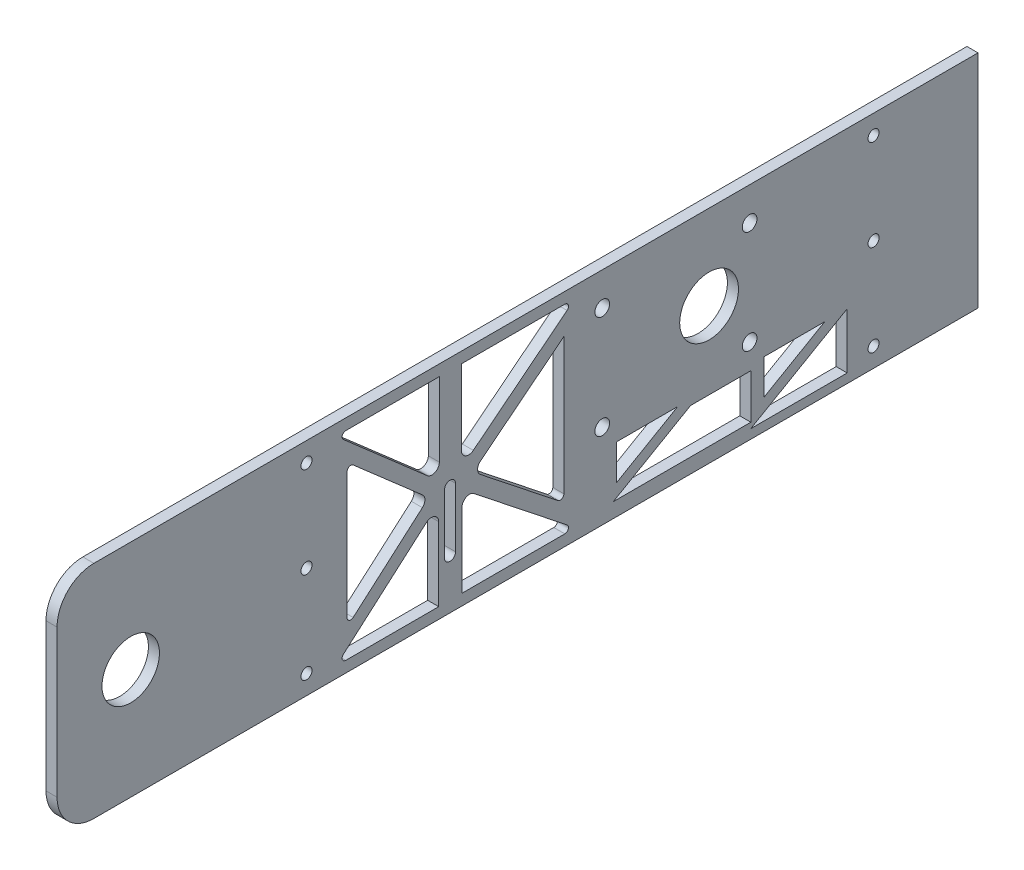
SolidWorks part; units mm, degrees
material "6061 Alloy"
ref_plane "Front Plane" through (0, 0, 0) normal (0, 0, 1) x (1, 0, 0)
ref_plane "Top Plane" through (0, 0, 0) normal (0, 1, 0) x (1, 0, 0)
ref_plane "Right Plane" through (0, 0, 0) normal (1, 0, 0) x (0, 0, -1)
sketch "Sketch1" plane through (0, 0, 0) normal (0, 0, 1) x (1, 0, 0)
  line L1 (1.5, -30) -> (-1.5, -30)
  line L2 (1.5, -30) -> (1.5, 30)
  line L3 (1.5, 30) -> (-1.5, 30)
  line L4 (-1.5, -30) -> (-1.5, 30)
  line L5 (1.5, -30) -> (-1.5, 30) construction
  line L6 (1.5, 30) -> (-1.5, -30) construction
  point P0 (0, 0)
  dimension "D1" = 60
  dimension "D2" = 3
extrude "Boss-Extrude1" add sketch "Sketch1" along normal blind 250
fillet "Fillet1" radius 10 1 edges at (0, 30, 250)
fillet "Fillet2" radius 10 1 edges at (0, -30, 250)
sketch "Sketch2" plane through (-1.5, 0, 0) normal (-1, 0, 0) x (0, 0, 1)
  line L0 (250, 0) -> (230, 0)
  line L1 (250, 20) -> (250, -20) construction
  circle A0 centre (230, 0) radius 4.25
extrude "Cut-Extrude1" cut sketch "Sketch2" against normal through all
sketch "Sketch3" plane through (1.5, 0, 0) normal (1, 0, 0) x (0, 0, -1)
  circle A0 centre (-10.5, 12.5) radius 2
  circle A1 centre (-10.5, 0) radius 2
  circle A2 centre (-10.5, -12.5) radius 2
sketch "Sketch5" plane through (-1.5, 0, 0) normal (-1, 0, 0) x (0, 0, 1)
  circle A0 centre (230, 0) radius 7.8
  dimension "D1" = 15.6
extrude "Cut-Extrude4" cut sketch "Sketch5" against normal through all
sketch "Sketch13" plane through (-1.5, 0, 0) normal (-1, 0, 0) x (0, 0, 1)
  line L0 (0, 30) -> (0, 0)
  line L1 (0, 30) -> (0, 7) construction
  line L2 (0, 7) -> (73, 7) construction
  circle A0 centre (73, 7) radius 7.98
extrude "Cut-Extrude10" cut sketch "Sketch13" against normal through all contours A0
sketch "Sketch14" plane through (1.5, 0, 0) normal (1, 0, 0) x (0, 0, -1)
  circle A0 centre (-102, -7) radius 2
  circle A1 centre (-102, 21) radius 2
  circle A2 centre (-62, 21) radius 2
  circle A3 centre (-62, -7) radius 2
  dimension "D1" = 4
extrude "Cut-Extrude11" cut sketch "Sketch14" against normal through all
sketch "Sketch17" plane through (-1.5, 0, 0) normal (-1, 0, 0) x (0, 0, 1)
  line L0 (240, -30) -> (0, -30) construction
  line L1 (174.2886, -27) -> (109.2886, -27)
  line L2 (174.2886, -27) -> (174.2886, 27)
  line L3 (174.2886, 27) -> (109.2886, 27)
  line L4 (109.2886, -27) -> (109.2886, 27)
  line L5 (240, 30) -> (0, 30) construction
  line L6 (179.2886, -33) -> (179.2886, 33) construction
  line L7 (174.2886, -27) -> (143.3777, 0)
  line L8 (143.3777, 0) -> (174.2886, 27)
  line L9 (174.2886, -22) -> (149.1019, 0)
  line L10 (149.1019, 0) -> (174.2886, 22)
  line L11 (143.3777, 0) -> (109.2886, -27)
  line L12 (143.3777, 0) -> (109.2886, 27)
  line L13 (109.2886, 22) -> (137.0649, 0)
  line L14 (137.0649, 0) -> (109.2886, -22)
  line L15 (146.2209, 2.4835) -> (140.2421, 2.4835)
  line L16 (146.3903, -2.6314) -> (140.0554, -2.6314)
  line L17 (146.3903, -2.6314) -> (146.3903, -27)
  line L18 (140.0554, -2.6314) -> (140.0554, -27)
  line L19 (140.2421, 2.4835) -> (140.2421, 27)
  line L20 (146.2209, 2.4835) -> (146.2209, 27)
  line L21 (171.276, -19.3686) -> (171.276, 19.3686)
  line L22 (112.4242, -19.5165) -> (112.4242, 19.5165)
  dimension "D1" = 3
  dimension "D2" = 3
  dimension "D3" = 5
  dimension "D4" = 65
  dimension "D5" = 5
  dimension "D6" = 5
  dimension "D7" = 5
  dimension "D8" = 5
  dimension "D9" = 4
  dimension "D10" = 4
  dimension "D11" = 4
  dimension "D12" = 4
extrude "Cut-Extrude14" cut sketch "Sketch17" against normal blind 10 contours L9 L21 L10 | L7 L17 L1 | L18 L11 L1 | L22 L14 L13 | L12 L19 L3 | L20 L8 L3
fillet "Fillet3" radius 1 7 edges at (0, -27, 174.2886) (0, -27, 109.2886) (0, -19.5165, 112.4242) (0, 27, 109.2886) (0, 27, 174.2886) (0, 19.3686, 171.276) (0, -19.3686, 171.276)
fillet "Fillet4" radius 2 6 edges at (0, 0, 149.1019) (0, 2.4835, 146.2209) (0, 2.4835, 140.2421) (0, 0, 137.0649) (0, -2.6314, 140.0554) (0, -2.6314, 146.3903)
sketch "Sketch18" plane through (-1.5, 0, 0) normal (-1, 0, 0) x (0, 0, 1)
  line L0 (105.9963, -27.5) -> (35.5082, -27.5)
  line L1 (35.5082, -27.5) -> (35.5082, -12.3962)
  line L2 (35.5082, -12.3962) -> (105.9963, -12.3962)
  line L3 (105.9963, -12.3962) -> (105.9963, -27.5)
  line L4 (101.5865, -27.5) -> (101.5865, -12.3962)
  line L5 (101.5865, -12.3962) -> (98.0865, -12.3962)
  line L6 (98.0865, -12.3962) -> (98.0865, -21.955)
  line L7 (98.0865, -21.955) -> (81.53, -12.3962)
  line L8 (81.53, -12.3962) -> (75.4258, -12.3962)
  line L9 (75.4258, -12.3962) -> (101.5865, -27.5)
  line L10 (61.6681, -27.5) -> (61.6681, -12.3962)
  line L11 (61.6681, -12.3962) -> (58.1438, -12.3962)
  line L12 (58.1438, -12.3962) -> (58.1438, -21.941)
  line L13 (58.1438, -21.941) -> (41.6122, -12.3962)
  line L14 (41.6122, -12.3962) -> (35.5082, -12.3962)
  line L15 (61.6681, -27.5) -> (35.5082, -12.3962)
  line L16 (78.0239, -13.8962) -> (61.6681, -13.8962)
  line L17 (98.9884, -26) -> (61.6681, -26)
  dimension "D1" = 1.5
  dimension "D2" = 1.5
extrude "Cut-Extrude18" cut sketch "Sketch18" against normal blind 10 contours L17 L9 L16 L10 | L7 L6 L2 | L13 L12 L2 | L0 L15 L1
sketch "Sketch19" plane through (-1.5, 0, 0) normal (-1, 0, 0) x (0, 0, 1)
  line L0 (143.3153, -0.2905) -> (143.3153, -16.3836) construction
  line L1 (143.3153, -25.8593) -> (143.3153, -6.9078) construction
  line L2 (144.8153, -0.2905) -> (144.8153, -16.3836)
  line L3 (141.8153, -0.2905) -> (141.8153, -16.3836)
  arc A0 (144.8153, -0.2905) -> (141.8153, -0.2905) centre (143.3153, -0.2905) ccw
  arc A1 (141.8153, -16.3836) -> (144.8153, -16.3836) centre (143.3153, -16.3836) ccw
  point P5 (143.3153, -8.337)
  dimension "D1" = 3
extrude "Cut-Extrude19" cut sketch "Sketch19" against normal through all contours L3 A1 L2 A0
sketch "Sketch20" plane through (-1.5, 0, 0) normal (-1, 0, 0) x (0, 0, 1)
  circle A0 centre (28.3518, -24.75) radius 1.5
  circle A1 centre (28.3518, 0) radius 1.5
  circle A2 centre (28.3518, 24.75) radius 1.5
  circle A3 centre (182.2886, -24.75) radius 1.5
  circle A4 centre (182.2886, 0) radius 1.5
  circle A5 centre (182.2886, 24.75) radius 1.5
extrude "Cut-Extrude20" cut sketch "Sketch20" against normal through all
